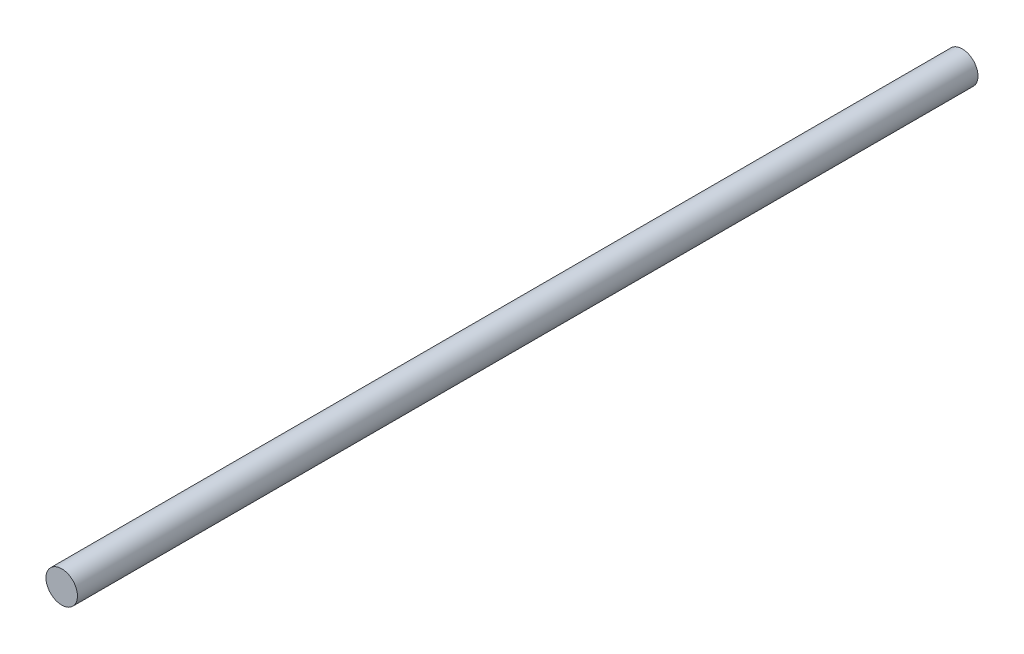
SolidWorks part; units mm, degrees
material "AISI Acero para herramientas tipo A2"
ref_plane "Alzado" through (0, 0, 0) normal (0, 0, 1) x (1, 0, 0)
ref_plane "Planta" through (0, 0, 0) normal (0, 1, 0) x (1, 0, 0)
ref_plane "Vista lateral" through (0, 0, 0) normal (1, 0, 0) x (0, 0, -1)
sketch "Croquis1" plane through (0, 0, 0) normal (0, 0, 1) x (1, 0, 0)
  circle A0 centre (0, 0) radius 5
  dimension "D1" = 10
extrude "Saliente-Extruir1" add sketch "Croquis1" along normal blind 286
